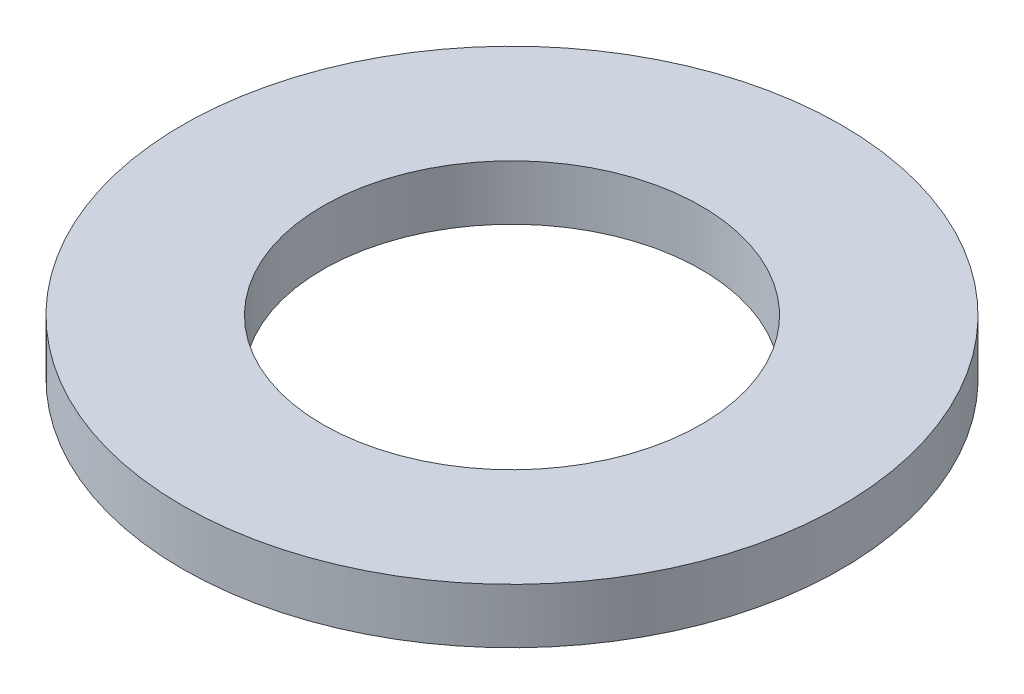
SolidWorks part; units mm, degrees
ref_plane "Front Plane" through (0, 0, 0) normal (0, 0, 1) x (1, 0, 0)
ref_plane "Top Plane" through (0, 0, 0) normal (0, 1, 0) x (1, 0, 0)
ref_plane "Right Plane" through (0, 0, 0) normal (1, 0, 0) x (0, 0, -1)
sketch "Sketch1" plane through (0, 0, 0) normal (0, 1, 0) x (1, 0, 0)
  circle A0 centre (0, 0) radius 1.524
  circle A1 centre (0, 0) radius 0.875
  dimension "D1" = 1.75
  dimension "D2" = 3.048
extrude "Boss-Extrude1" add sketch "Sketch1" along normal blind 0.254
